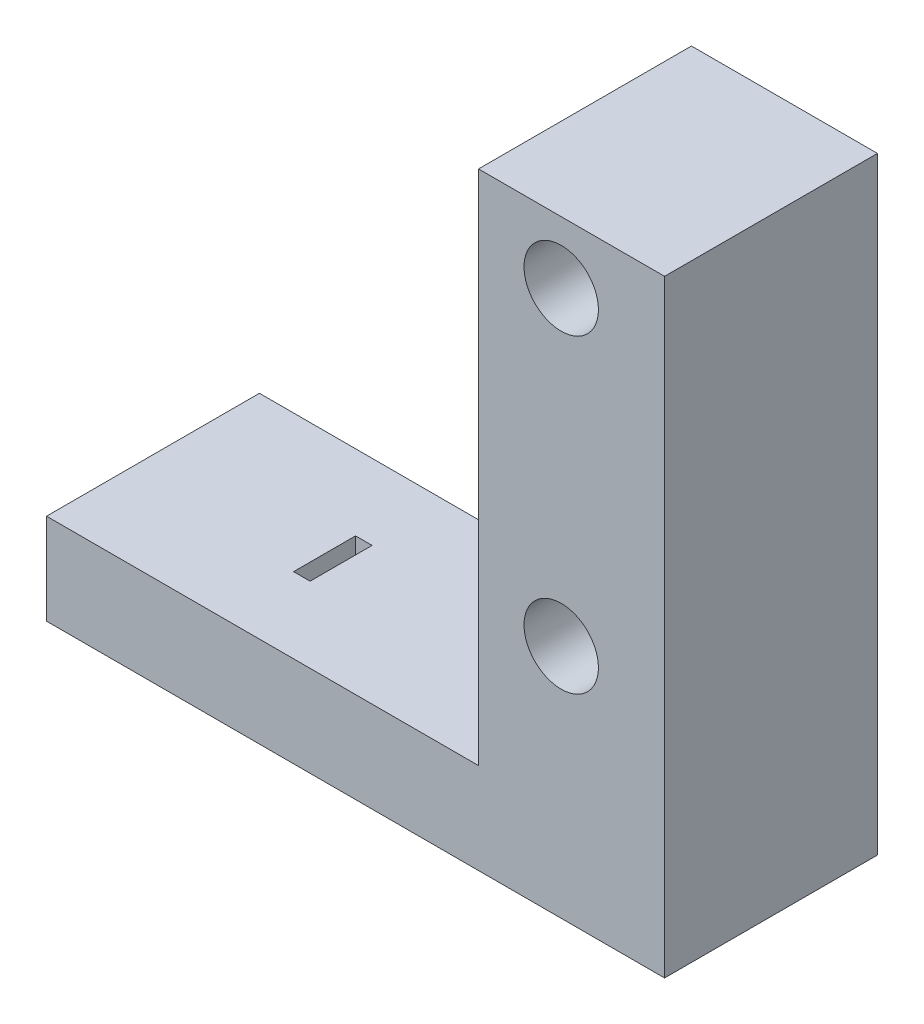
SolidWorks part; units mm, degrees
ref_plane "Front Plane" through (0, 0, 0) normal (0, 0, 1) x (1, 0, 0)
ref_plane "Top Plane" through (0, 0, 0) normal (0, 1, 0) x (1, 0, 0)
ref_plane "Right Plane" through (0, 0, 0) normal (1, 0, 0) x (0, 0, -1)
sketch "Sketch1" plane through (0, 0, 0) normal (0, 1, 0) x (1, 0, 0)
  line L0 (-14.25, 0) -> (0, 0) construction
  line L2 (-20.25, 5.15) -> (9.65, 5.15)
  line L3 (-20.25, 5.15) -> (-20.25, -5.15)
  line L4 (-20.25, -5.15) -> (9.65, -5.15)
  line L5 (9.65, 5.15) -> (9.65, -5.15)
  line L6 (-5.3, -5.15) -> (-5.3, 5.15) construction
  line L7 (-20.25, 0) -> (9.65, 0) construction
  circle A0 centre (0, 0) radius 2.4
  circle A1 centre (-14.25, 0) radius 2.4
  point P157 (-5.3, 0)
  dimension "D2" = 4.8
  dimension "D3" = 9.65
  dimension "D1" = 14.25
  dimension "D4" = 10.3
  dimension "D5" = 6
extrude "Boss-Extrude1" add sketch "Sketch1" along normal blind 30
sketch "Sketch4" plane through (0, 0, 0) normal (0, -1, 0) x (1, 0, 0)
  line L1 (-20.25, 5.15) -> (9.65, 5.15)
  line L2 (-20.25, 5.15) -> (-20.25, -5.15)
  line L3 (-20.25, -5.15) -> (9.65, -5.15)
  line L4 (9.65, 5.15) -> (9.65, -5.15)
  line L5 (-5.3, -5.15) -> (-5.3, 5.15) construction
  line L6 (-20.25, 0) -> (9.65, 0) construction
  point P268 (-5.3, 0)
extrude "Boss-Extrude3" add sketch "Sketch4" against normal up to surface (28 mm away) from offset 2 up to face at (0, 30, 2.4) offset against normal yes
sketch "Sketch2" plane through (0, 0, 5.15) normal (0, 0, 1) x (1, 0, 0)
  line L0 (9.65, 30) -> (9.65, 0) construction
  line L1 (-20.25, 30) -> (0.65, 30)
  line L2 (-20.25, 30) -> (-20.25, 5)
  line L3 (-20.25, 5) -> (0.65, 5)
  line L4 (0.65, 30) -> (0.65, 5)
  line L5 (-9.8, 5) -> (-9.8, 30) construction
  line L6 (-20.25, 17.5) -> (0.65, 17.5) construction
  line L7 (-20.25, 0) -> (9.65, 0) construction
  point P320 (-9.8, 17.5)
  dimension "D1" = 9
  dimension "D2" = 5
extrude "Cut-Extrude1" cut sketch "Sketch2" against normal through all
sketch "Sketch3" plane through (0, 0, 0) normal (0, -1, 0) x (1, 0, 0)
  line L0 (-2.2, 0) -> (0, 0) construction
  line L1 (-11.95, 1.5) -> (-11.15, 1.5)
  line L2 (-11.95, 1.5) -> (-11.95, -1.5)
  line L3 (-11.95, -1.5) -> (-11.15, -1.5)
  line L4 (-11.15, 1.5) -> (-11.15, -1.5)
  line L5 (-11.55, -1.5) -> (-11.55, 1.5) construction
  line L6 (-11.95, 0) -> (-11.15, 0) construction
  line L7 (-3, 1.5) -> (-2.2, 1.5)
  line L8 (-3, 1.5) -> (-3, -1.5)
  line L9 (-3, -1.5) -> (-2.2, -1.5)
  line L10 (-2.2, 1.5) -> (-2.2, -1.5)
  line L11 (-2.6, -1.5) -> (-2.6, 1.5) construction
  line L12 (-3, 0) -> (-2.2, 0) construction
  circle A0 centre (0, 0) radius 2.4 construction
  circle A1 centre (-14.25, 0) radius 2.4 construction
  point P136 (-11.55, 0)
  point P157 (-2.6, 0)
  dimension "D1" = 0.8
  dimension "D2" = 3
  dimension "D3" = 0.2
  dimension "D4" = 0.1
extrude "Cut-Extrude2" cut sketch "Sketch3" against normal through all
hole_wizard "M3 Clearance Hole1" positions "Sketch5" profile "Sketch6" hole size "M3" standard "ANSI Metric" end condition through all
sketch "Sketch5" plane through (0, 0, 5.15) normal (0, 0, 1) x (1, 0, 0)
  line L0 (9.65, 30) -> (9.65, 0) construction
  line L1 (4.65, 27) -> (4.65, 12) construction
  point P0 (4.65, 12)
  point P2 (4.65, 27)
  dimension "D1" = 15
  dimension "D2" = 5
  dimension "D3" = 12
sketch "Sketch6" plane through (4.65, 12, 5.15) normal (1, 0, 0) x (0, -1, 0)
  line L0 (0, 0) -> (0, 10.3)
  line L1 (0, 10.3) -> (1.8, 10.3)
  line L2 (1.8, 10.3) -> (1.8, 0)
  line L5 (1.8, 0) -> (0, 0)
  line L11 (0, -6.35) -> (0, 107.95) construction
  dimension "Thru Hole Dia." = 3.6
  dimension "Thru Hole Depth" = 10.3
sketch "Sketch7" plane through (0, 0, 0) normal (0, -1, 0) x (1, 0, 0)
  line L0 (-3, -1.5) -> (-2.2, -1.5) construction
  line L1 (-11.15, 1.5) -> (-12.3765, 1.5)
  line L2 (-11.15, 1.5) -> (-11.15, -1.5)
  line L3 (-11.15, -1.5) -> (-12.3765, -1.5)
  line L4 (-12.3765, 1.5) -> (-12.3765, -1.5)
  line L5 (-11.7633, -1.5) -> (-11.7633, 1.5) construction
  line L6 (-11.15, 0) -> (-12.3765, 0) construction
  line L7 (-3, 1.5) -> (-1.8735, 1.5)
  line L8 (-3, 1.5) -> (-3, -1.5)
  line L9 (-3, -1.5) -> (-1.8735, -1.5)
  line L10 (-1.8735, 1.5) -> (-1.8735, -1.5)
  line L11 (-2.4367, -1.5) -> (-2.4367, 1.5) construction
  line L12 (-3, 0) -> (-1.8735, 0) construction
  line L13 (-3, 1.5) -> (-3, -1.5) construction
  arc A0 (-2.2, -0.9592) -> (-2.2, 0.9592) centre (0, 0) ccw construction
  arc A1 (-11.95, 0.6856) -> (-11.95, -0.6856) centre (-14.25, 0) ccw construction
  point P92 (-2.4367, 0)
  point P336 (-11.7633, 0)
extrude "Cut-Extrude3" cut sketch "Sketch7" against normal up to surface (2 mm away) up to face at (-14.3, 2, 0)
sketch "Sketch8" plane through (0, 0, 0) normal (0, -1, 0) x (1, 0, 0)
  line L1 (-15.6356, 2.4) -> (-17.0213, 0)
  line L2 (-17.0213, 0) -> (-15.6356, -2.4)
  line L3 (-15.6356, -2.4) -> (-12.8644, -2.4)
  line L4 (-12.8644, -2.4) -> (-11.4787, 0)
  line L5 (-11.4787, 0) -> (-12.8644, 2.4)
  line L6 (-12.8644, 2.4) -> (-15.6356, 2.4)
  line L7 (1.3856, 2.4) -> (-1.3856, 2.4)
  line L8 (-1.3856, 2.4) -> (-2.7713, 0)
  line L9 (-2.7713, 0) -> (-1.3856, -2.4)
  line L10 (-1.3856, -2.4) -> (1.3856, -2.4)
  line L11 (1.3856, -2.4) -> (2.7713, 0)
  line L12 (2.7713, 0) -> (1.3856, 2.4)
  circle A0 centre (-14.25, 0) radius 2.4 construction
  circle A1 centre (0, 0) radius 2.4 construction
  arc A2 (-1.8735, -1.5) -> (-1.8735, 1.5) centre (0, 0) ccw construction
  arc A3 (-12.3765, 1.5) -> (-12.3765, -1.5) centre (-14.25, 0) ccw construction
extrude "Cut-Extrude4" cut sketch "Sketch8" against normal up to surface (2 mm away) up to face at (-13.2316, 2, 0)
chamfer "Chamfer1" distance 0.6 angle 45 22 edges at (-11.7474, 0, -1.5) (-11.15, 0, 0) (-11.7474, 0, 1.5) (-2.4526, 0, -1.5) (-2.4526, 0, 1.5) (-3, 0, 0) (-5.3, 0, 5.15) (9.65, 0, 0) (-5.3, 0, -5.15) (-20.25, 0, 0) (-16.3285, 0, 1.2) (-16.3285, 0, -1.2) (-14.25, 0, -2.4) (-12.6046, 0, -1.95) (-12.6046, 0, 1.95) (-14.25, 0, 2.4) (2.0785, 0, -1.2) (2.0785, 0, 1.2) (0, 0, 2.4) (-1.6454, 0, 1.95) (-1.6454, 0, -1.95) (0, 0, -2.4)
